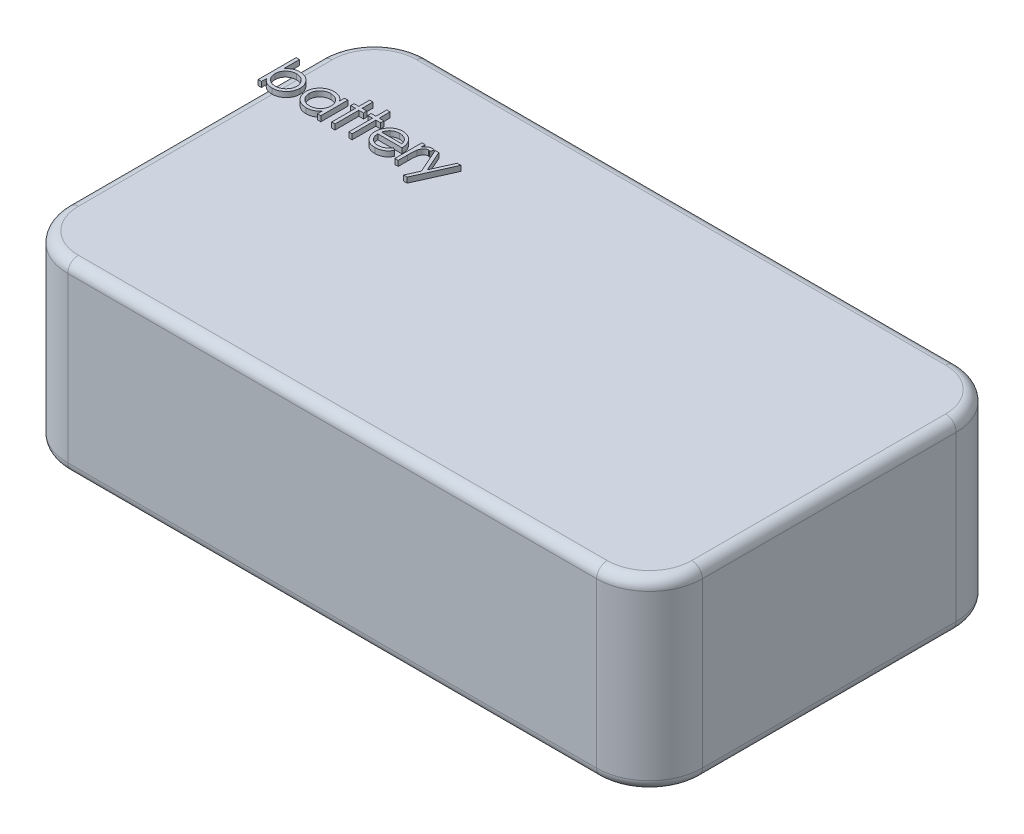
SolidWorks part; units mm, degrees
ref_plane "Front Plane" through (0, 0, 0) normal (0, 0, 1) x (1, 0, 0)
ref_plane "Top Plane" through (0, 0, 0) normal (0, 1, 0) x (1, 0, 0)
ref_plane "Right Plane" through (0, 0, 0) normal (1, 0, 0) x (0, 0, -1)
sketch "Sketch1" plane through (0, 0, 0) normal (0, 1, 0) x (1, 0, 0)
  line L1 (-30, 17) -> (30, 17)
  line L2 (-30, 17) -> (-30, -17)
  line L3 (-30, -17) -> (30, -17)
  line L4 (30, 17) -> (30, -17)
  line L5 (-30, 17) -> (30, -17) construction
  line L6 (-30, -17) -> (30, 17) construction
  point P0 (0, 0)
  dimension "D1" = 60
  dimension "D2" = 34
extrude "Boss-Extrude1" add sketch "Sketch1" along normal blind 17.5
fillet "Fillet1" radius 5 4 edges at (-30, 8.75, -17) (30, 8.75, -17) (30, 8.75, 17) (-30, 8.75, 17)
fillet "Fillet2" radius 1 16 edges at (28.5355, 17.5, -15.5355) (30, 17.5, 0) (28.5355, 17.5, 15.5355) (-28.5355, 17.5, 15.5355) (-30, 17.5, 0) (-28.5355, 17.5, -15.5355) (28.5355, 0, -15.5355) (30, 0, 0) (28.5355, 0, 15.5355) (-28.5355, 0, 15.5355) (-30, 0, 0) (-28.5355, 0, -15.5355) (0, 17.5, 17) (0, 0, 17) (0, 17.5, -17) (0, 0, -17)
sketch "Sketch2" plane through (0, 17.5, 0) normal (0, 1, 0) x (1, 0, 0)
  text T0 "battery\r\n"
extrude "Boss-Extrude2" add sketch "Sketch2" along normal blind 0.5
